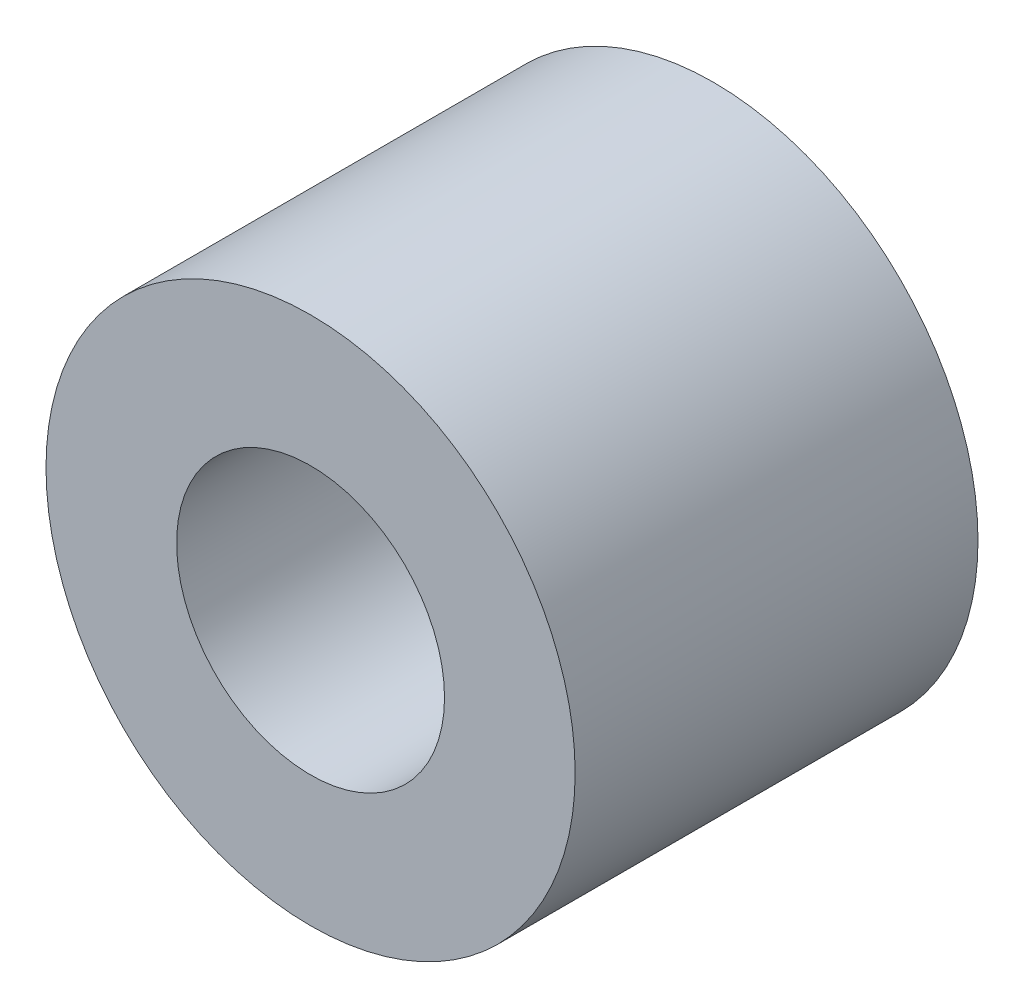
SolidWorks part; units mm, degrees
ref_plane "Front Plane" through (0, 0, 0) normal (0, 0, 1) x (1, 0, 0)
ref_plane "Top Plane" through (0, 0, 0) normal (0, 1, 0) x (1, 0, 0)
ref_plane "Right Plane" through (0, 0, 0) normal (1, 0, 0) x (0, 0, -1)
sketch "Sketch1" plane through (0, 0, 0) normal (0, 0, 1) x (1, 0, 0)
  circle A0 centre (0, 0) radius 3.75
  dimension "D1" = 7.5
extrude "Boss-Extrude1" add sketch "Sketch1" along normal mid plane 5.71
hole_wizard "#10-24 Tapped Hole1" positions "Sketch2" profile "Sketch3" tap size "#10-24" standard "ANSI Inch" end condition through all
sketch "Sketch2" plane through (0, 0, 2.855) normal (0, 0, 1) x (1, 0, 0)
  point P0 (0, 0)
sketch "Sketch3" plane through (0, 0, 2.855) normal (1, 0, 0) x (0, -1, 0)
  line L0 (0, 0) -> (0, 5.71)
  line L1 (0, 5.71) -> (1.8986, 5.71)
  line L2 (1.8986, 5.71) -> (1.8986, 0)
  line L5 (1.8986, 0) -> (0, 0)
  line L11 (0, -6.35) -> (0, 107.95) construction
  dimension "Thru Tap Drill Dia." = 3.7973
  dimension "Thru Tap Drill Depth" = 5.71
cosmetic thread "Hole Thread1"
